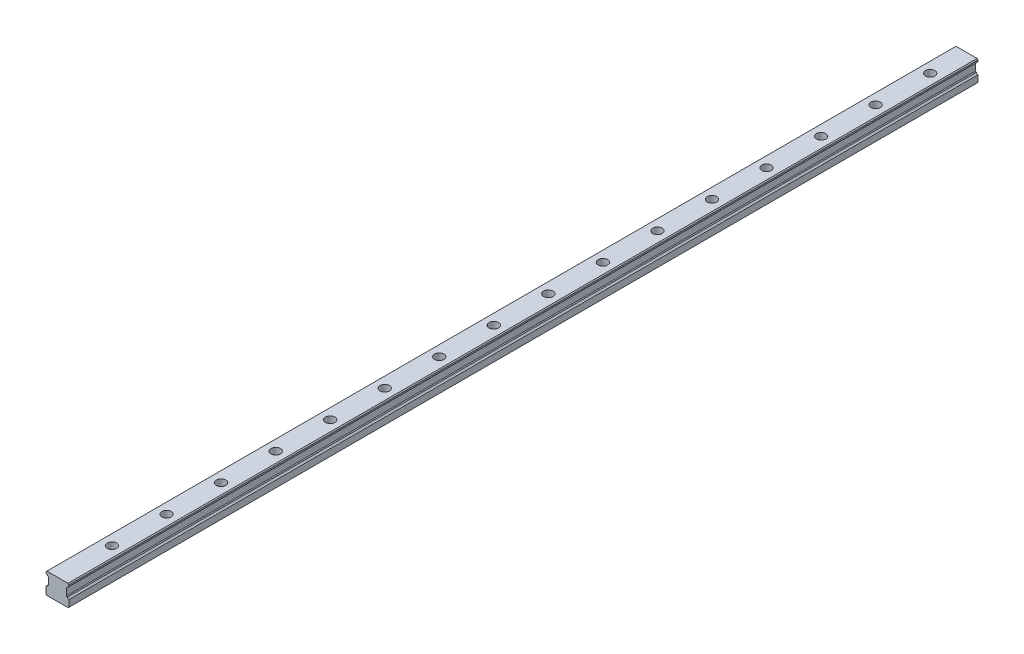
SolidWorks part; units mm, degrees
ref_plane "Plano frontal" through (0, 0, 0) normal (0, 0, 1) x (1, 0, 0)
ref_plane "Plano superior" through (0, 0, 0) normal (0, 1, 0) x (1, 0, 0)
ref_plane "Plano direito" through (0, 0, 0) normal (1, 0, 0) x (0, 0, -1)
sketch "Esboço1" plane through (0, 0, 0) normal (0, 0, 1) x (1, 0, 0)
  line L0 (-31.5, 20.5273) -> (-31.5, 0)
  line L1 (-31.5, 0) -> (31.5, 0)
  line L2 (31.5, 0) -> (31.5, 20.5273)
  line L3 (27.3973, 24.8216) -> (24.5, 25.5979)
  line L4 (24.5, 25.5979) -> (24.5, 46.3977)
  line L5 (24.5, 46.3977) -> (27.3971, 47.1739)
  line L6 (31.5, 51.4749) -> (31.5, 58)
  line L7 (31.5, 58) -> (-31.5, 58)
  line L8 (-31.5, 58) -> (-31.5, 51.4749)
  line L9 (-27.3978, 47.1758) -> (-24.5, 46.3997)
  line L10 (-24.5, 46.3997) -> (-24.5, 25.597)
  line L11 (-24.5, 25.597) -> (-27.3979, 24.8234)
  arc A0 (-27.3979, 24.8234) -> (-31.5, 20.5273) centre (-33.3777, 26.4267) cw
  arc A1 (31.5, 20.5273) -> (27.3973, 24.8216) centre (33.3765, 26.4271) cw
  arc A2 (27.3971, 47.1739) -> (31.5, 51.4749) centre (33.3782, 45.5757) cw
  arc A3 (-31.5, 51.4749) -> (-27.3978, 47.1758) centre (-33.3784, 45.5757) cw
extrude "Ressalto-extrusão1" add sketch "Esboço1" along normal blind 2500
hole_wizard "Rebaixo para parafuso de cabeça sextavada de M161" positions "Esboço3" profile "Esboço2" counterbore size "M16" standard "Ansi Metric"
sketch "Esboço3" plane through (0, 58, 0) normal (0, 1, 0) x (1, 0, 0)
  line L0 (0, -100) -> (0, 0) construction
  line L1 (31.5, 0) -> (-31.5, 0) construction
  point P0 (0, -100)
  point P23 (0, -250)
  point P24 (0, -400)
  point P25 (0, -550)
  point P26 (0, -700)
  point P27 (0, -850)
  point P28 (0, -1000)
  point P29 (0, -1150)
  point P30 (0, -1300)
  point P31 (0, -1450)
  point P32 (0, -1600)
  point P33 (0, -1750)
  point P34 (0, -1900)
  point P35 (0, -2050)
  point P36 (0, -2200)
  point P37 (0, -2350)
  dimension "D1" = 100
  dimension "D2" = 16
sketch "Esboço2" plane through (0, 58, 100) normal (1, 0, 0) x (0, 0, 1)
  line L0 (0, 0) -> (0, 58)
  line L1 (0, 58) -> (9, 58)
  line L3 (9, 58) -> (9, 25)
  line L4 (9, 25) -> (13, 25)
  line L5 (13, 25) -> (13, 0)
  line L7 (13, 0) -> (0, 0)
  line L11 (0, -6.35) -> (0, 107.95) construction
  dimension "Thru Hole Dia." = 18
  dimension "Thru Hole Depth" = 58
  dimension "C'Bore Dia." = 26
  dimension "C'Bore Depth" = 25
chamfer "Chanfro1" distance 2.5003 angle 45 1 edges at (-31.5, 58, 1250)
chamfer "Chanfro2" distance 2.5003 angle 45.002 1 edges at (31.5, 58, 1250)
chamfer "Chanfro3" distance 2 angle 45 2 edges at (31.5, 0, 1250) (-31.5, 0, 1250)
